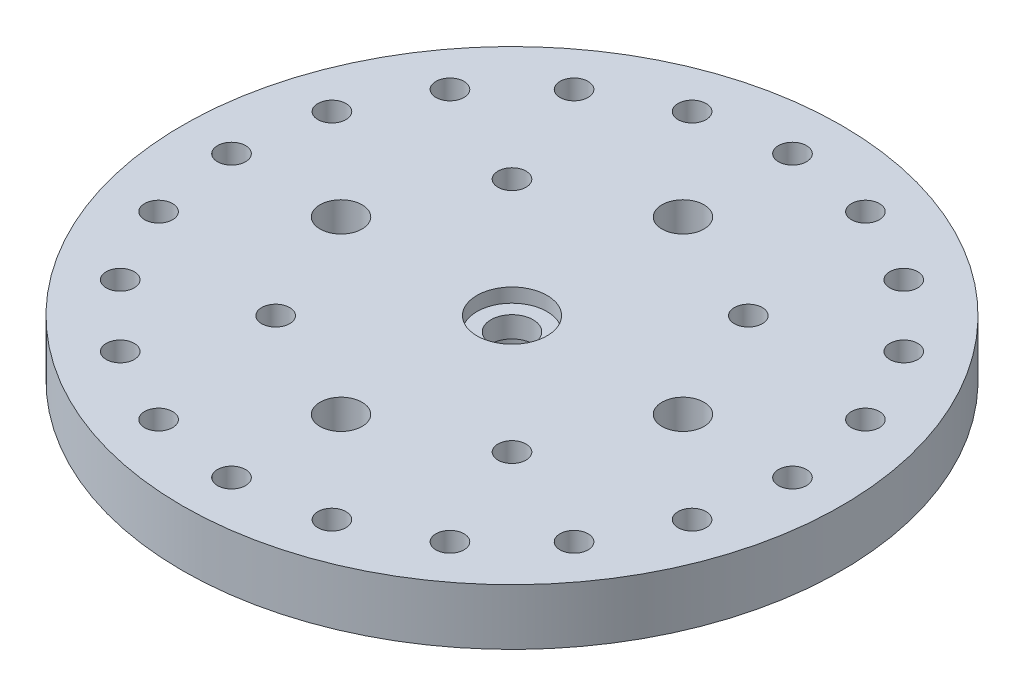
SolidWorks part; units mm, degrees
ref_plane "Front Plane" through (0, 0, 0) normal (0, 0, 1) x (1, 0, 0)
ref_plane "Top Plane" through (0, 0, 0) normal (0, 1, 0) x (1, 0, 0)
ref_plane "Right Plane" through (0, 0, 0) normal (1, 0, 0) x (0, 0, -1)
sketch "Sketch1" plane through (0, 0, 0) normal (0, 1, 0) x (1, 0, 0)
  circle A0 centre (0, 0) radius 23.5
  circle A1 centre (0, 0) radius 1.5
  circle A2 centre (0, 20) radius 1
  circle A3 centre (6.1803, 19.0211) radius 1
  circle A4 centre (11.7557, 16.1803) radius 1
  circle A5 centre (16.1803, 11.7557) radius 1
  circle A6 centre (19.0211, 6.1803) radius 1
  circle A7 centre (20, 0) radius 1
  circle A8 centre (19.0211, -6.1803) radius 1
  circle A9 centre (16.1803, -11.7557) radius 1
  circle A10 centre (11.7557, -16.1803) radius 1
  circle A11 centre (6.1803, -19.0211) radius 1
  circle A12 centre (0, -20) radius 1
  circle A13 centre (-6.1803, -19.0211) radius 1
  circle A14 centre (-11.7557, -16.1803) radius 1
  circle A15 centre (-16.1803, -11.7557) radius 1
  circle A16 centre (-19.0211, -6.1803) radius 1
  circle A17 centre (-20, 0) radius 1
  circle A18 centre (-19.0211, 6.1803) radius 1
  circle A19 centre (-16.1803, 11.7557) radius 1
  circle A20 centre (-11.7557, 16.1803) radius 1
  circle A21 centre (-6.1803, 19.0211) radius 1
  circle A22 centre (0, 12.1919) radius 1.5
  circle A23 centre (12.1919, 0) radius 1.5
  circle A24 centre (0, -12.1919) radius 1.5
  circle A25 centre (-12.1919, 0) radius 1.5
  circle A26 centre (-8.4255, 8.4255) radius 1
  circle A27 centre (8.4255, 8.4255) radius 1
  circle A28 centre (8.4255, -8.4255) radius 1
  circle A29 centre (-8.4255, -8.4255) radius 1
  point P47 (0, 0)
  point P49 (0, 0)
  point P56 (0, 0)
  point P65 (0, 0)
  dimension "D1" = 47
  dimension "D2" = 3
  dimension "D3" = 2
  dimension "D5" = 3
  dimension "D7" = 2
  dimension "D8" = 45
  dimension "D10" = 20
  dimension "D4" = 20
  dimension "D6" = 4
  dimension "D9" = 4
extrude "Boss-Extrude1" add sketch "Sketch1" along normal blind 4
sketch "Sketch2" plane through (0, 0, 0) normal (0, -1, 0) x (1, 0, 0)
  circle A0 centre (0, 0) radius 2.7
  dimension "D1" = 5.4
extrude "Cut-Extrude1" cut sketch "Sketch2" against normal blind 1.5
sketch "Sketch3" plane through (0, 4, 0) normal (0, 1, 0) x (1, 0, 0)
  circle A0 centre (0, 0) radius 2.5
  dimension "D1" = 5
extrude "Cut-Extrude2" cut sketch "Sketch3" against normal blind 1
sketch "Sketch4" plane through (0, 0, 0) normal (0, -1, 0) x (1, 0, 0)
  circle A0 centre (0, 0) radius 2.7 construction
  circle A1 centre (0, 0) radius 2.7
extrude "Extrude-Thin1" add sketch "Sketch4" along normal blind 1 thin
